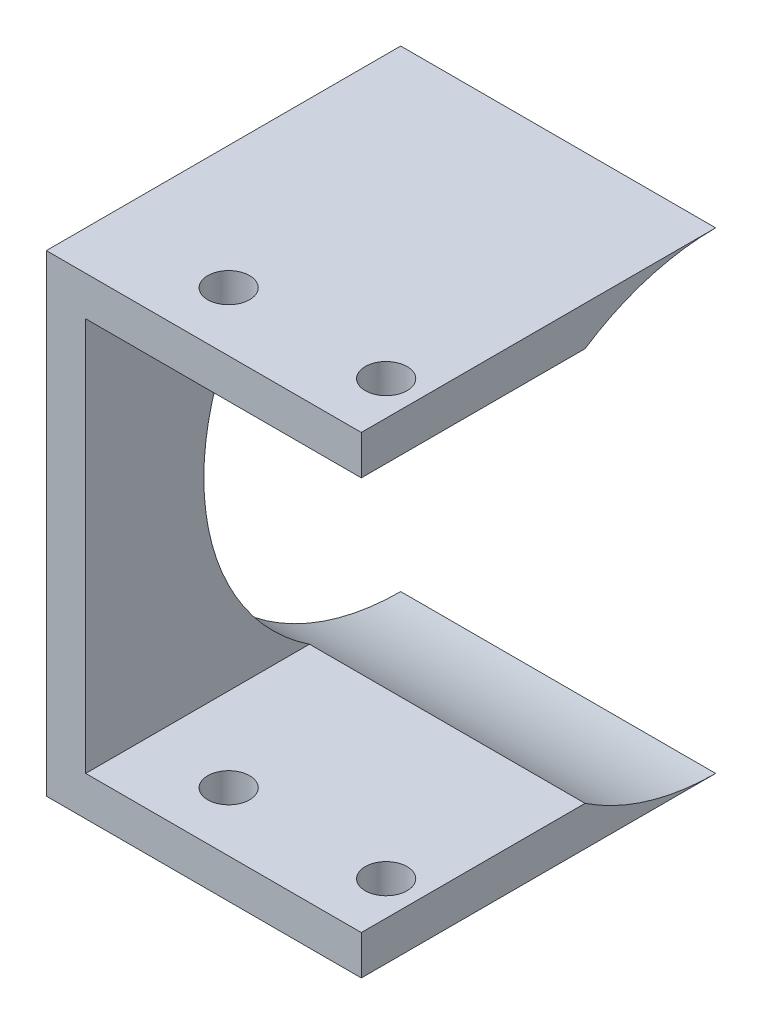
SolidWorks part; units mm, degrees
material "6061 Alloy"
ref_plane "Front Plane" through (0, 0, 0) normal (0, 0, 1) x (1, 0, 0)
ref_plane "Top Plane" through (0, 0, 0) normal (0, 1, 0) x (1, 0, 0)
ref_plane "Right Plane" through (0, 0, 0) normal (1, 0, 0) x (0, 0, -1)
sketch "Sketch2" plane through (0, 0, 0) normal (0, 0, 1) x (1, 0, 0)
  line L1 (0, 0) -> (50.8, 0)
  line L2 (0, 0) -> (0, 76.2)
  line L3 (0, 76.2) -> (50.8, 76.2)
  line L4 (50.8, 0) -> (50.8, 76.2)
  dimension "D1" = 50.8
  dimension "D2" = 76.2
extrude "Boss-Extrude2" add sketch "Sketch2" along normal blind 57.15
sketch "Sketch3" plane through (50.8, 0, 0) normal (1, 0, 0) x (0, 0, -1)
  line L0 (0, 0) -> (0, 76.2) construction
  circle A0 centre (0, 38.1) radius 38.1
  dimension "D1" = 76.2
extrude "Cut-Extrude1" cut sketch "Sketch3" against normal through all
shell "Shell1" thickness 6.35
hole_wizard "1/4 Clearance Hole1" positions "Sketch4" profile "Sketch5" hole size "1/4" standard "ANSI Inch" end condition through all
sketch "Sketch4" plane through (0, 76.2, 0) normal (0, 1, 0) x (1, 0, 0)
  line L1 (6.35, -57.15) -> (6.35, -21.0606) construction
  line L2 (6.35, -57.15) -> (6.35, -21.0606) construction
  line L3 (50.8, 0) -> (-16.465, 0) construction
  line L4 (50.8, -38.1) -> (50.8, 38.1) construction
  point P2 (45.2818, -47.625)
  point P11 (19.8819, -47.625)
  point P23 (0, 0)
  point P24 (12.4374, -38.1)
  dimension "D1" = 47.625
  dimension "D2" = 25.4
  dimension "D3" = 13.5318
sketch "Sketch5" plane through (45.2818, 76.2, 47.625) normal (1, 0, 0) x (0, 0, 1)
  line L0 (0, 0) -> (0, 76.2)
  line L1 (0, 76.2) -> (3.3782, 76.2)
  line L2 (3.3782, 76.2) -> (3.3782, 0)
  line L5 (3.3782, 0) -> (0, 0)
  line L11 (0, -6.35) -> (0, 107.95) construction
  dimension "Thru Hole Dia." = 6.7564
  dimension "Thru Hole Depth" = 76.2
